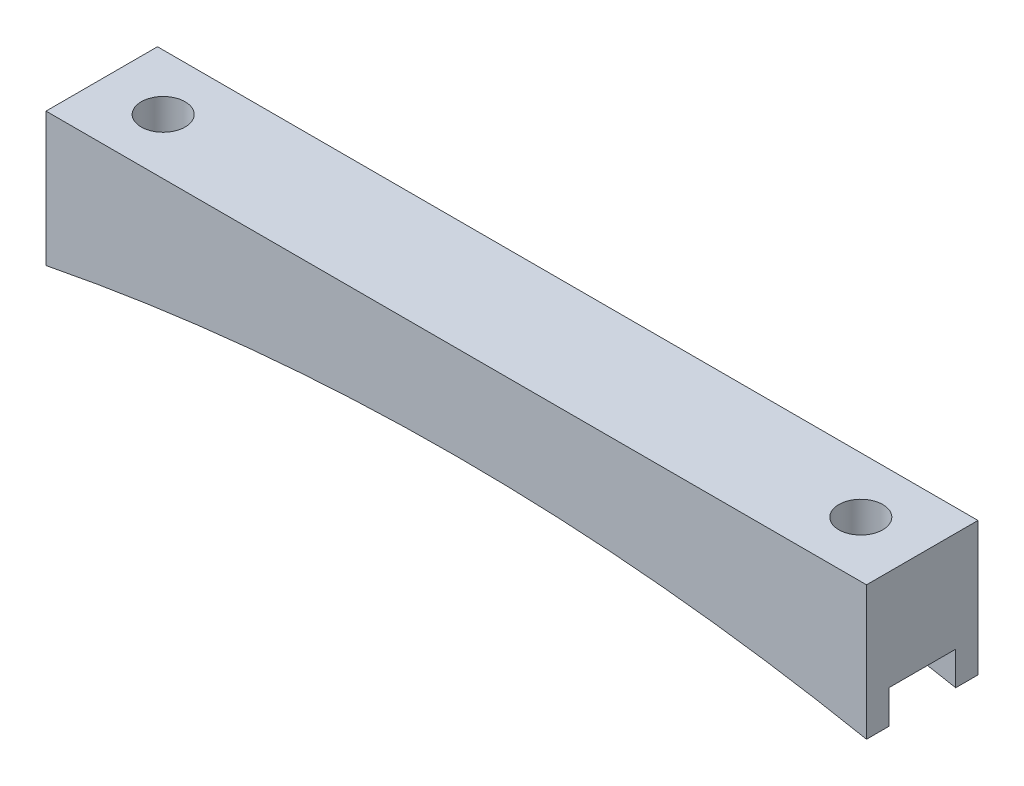
SolidWorks part; units mm, degrees
ref_plane "Front Plane" through (0, 0, 0) normal (0, 0, 1) x (1, 0, 0)
ref_plane "Top Plane" through (0, 0, 0) normal (0, 1, 0) x (1, 0, 0)
ref_plane "Right Plane" through (0, 0, 0) normal (1, 0, 0) x (0, 0, -1)
sketch "Sketch1" plane through (0, 0, 0) normal (0, 0, 1) x (1, 0, 0)
  line L0 (-46.735, 0) -> (46.735, 0)
  line L1 (-39.735, -2.54) -> (39.735, -2.54) construction
  line L2 (0, 0) -> (0, -4.6068) construction
  line L3 (46.735, 0) -> (46.735, -15.24)
  line L4 (-46.735, 0) -> (-46.735, -15.24)
  arc A0 (-46.735, -15.24) -> (46.735, -15.24) centre (0, -251.9709) cw
  point P4 (0, 0)
  point P9 (0, -2.54)
  dimension "D4" = 241.3
  dimension "D1" = 79.47
  dimension "D2" = 2.54
  dimension "D3" = 7
  dimension "D5" = 15.24
extrude "Boss-Extrude1" add sketch "Sketch1" along normal blind 12.7
sketch "Sketch2" plane through (0, 0, 0) normal (0, 1, 0) x (1, 0, 0)
  line L1 (-39.735, 0) -> (-39.735, -12.7) construction
  line L2 (-46.735, 0) -> (46.735, 0) construction
  line L3 (46.735, -12.7) -> (-46.735, -12.7) construction
  line L4 (39.735, 0) -> (39.735, -12.7) construction
  circle A0 centre (-39.735, -6.35) radius 2.5
  circle A1 centre (39.735, -6.35) radius 2.5
  circle A2 centre (-39.735, -6.35) radius 3 construction
  point P7 (-39.735, -6.35)
  dimension "D1" = 5
  dimension "D2" = 6
extrude "Cut-Extrude1" cut sketch "Sketch2" against normal through all
sketch "Sketch3" plane through (46.735, 0, 0) normal (1, 0, 0) x (0, 0, -1)
  line L0 (-12.7, -15.24) -> (0, -15.24) construction
  line L1 (-10.16, -15.24) -> (-2.54, -15.24)
  line L2 (-10.16, -15.24) -> (-10.16, -11.43)
  line L3 (-10.16, -11.43) -> (-2.54, -11.43)
  line L4 (-2.54, -15.24) -> (-2.54, -11.43)
  line L5 (-12.7, -15.24) -> (-12.7, 0) construction
  line L6 (0, -15.24) -> (0, 0) construction
  dimension "D1" = 2.54
  dimension "D2" = 2.54
  dimension "D3" = 3.81
extrude "Cut-Extrude2" cut sketch "Sketch3" against normal through all
